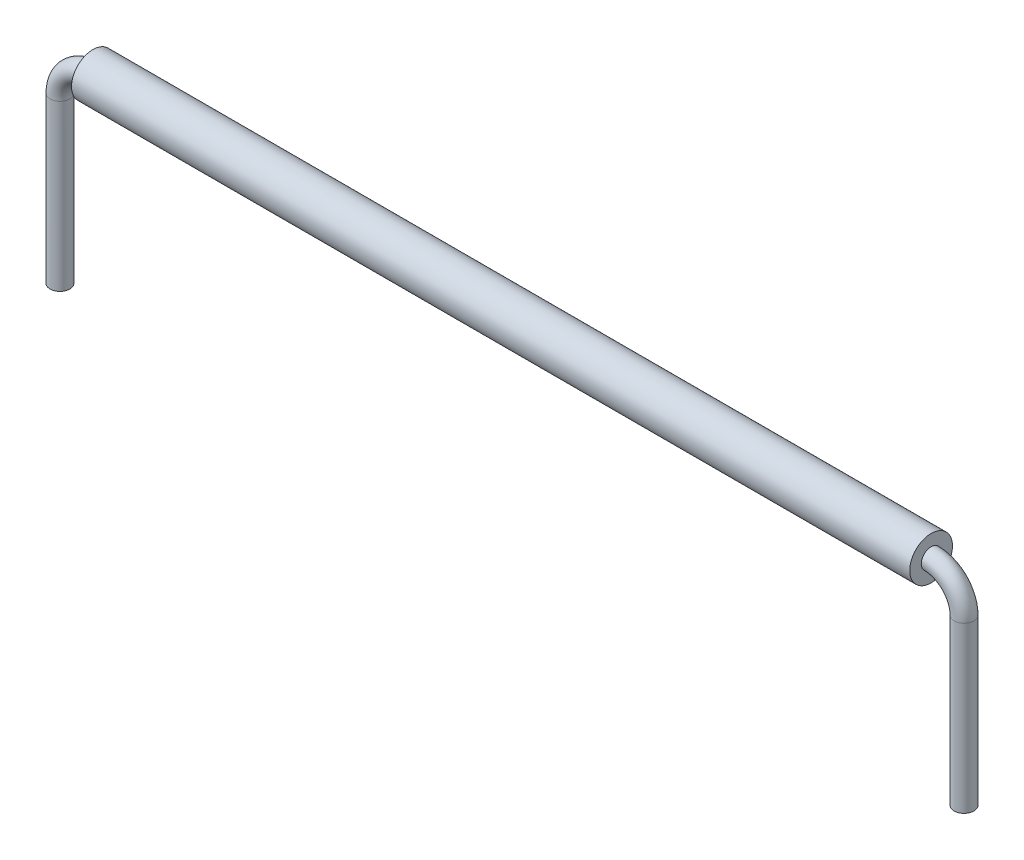
SolidWorks part; units mm, degrees
other "Insulation"
other "Wire"
ref_plane "Front Plane" through (0, 0, 0) normal (0, 0, 1) x (1, 0, 0)
ref_plane "Top Plane" through (0, 0, 0) normal (0, 1, 0) x (1, 0, 0)
ref_plane "Right Plane" through (0, 0, 0) normal (1, 0, 0) x (0, 0, -1)
sketch "Sketch1" plane through (0, 0, 0) normal (0, 0, 1) x (1, 0, 0)
  line L0 (-12.7275, 0) -> (12.7275, 0)
  line L1 (-13.7275, -1) -> (-13.7275, -6)
  line L2 (13.7275, -1) -> (13.7275, -6)
  line L3 (0, 0) -> (0, -6) construction
  line L4 (-13.7275, -6) -> (13.7275, -6) construction
  arc A0 (-12.7275, 0) -> (-13.7275, -1) centre (-12.7275, -1) ccw
  arc A1 (12.7275, 0) -> (13.7275, -1) centre (12.7275, -1) cw
  dimension "D1" = 1
  dimension "D2" = 27.455
  dimension "D3" = 6
sketch "Sketch2" plane through (0, 0, 0) normal (1, 0, 0) x (0, 0, -1)
  circle A0 centre (0, 0) radius 0.3
  dimension "D1" = 0.6
sweep "Sweep1" add profiles "Sketch2" path "Sketch1"
sketch "Sketch3" plane through (0, 0, 0) normal (1, 0, 0) x (0, 0, -1)
  circle A0 centre (0, 0) radius 0.65
  circle A1 centre (0, 0) radius 0.3
  dimension "D1" = 1.3
  dimension "D2" = 0.6
extrude "Boss-Extrude1" add sketch "Sketch3" along normal up to vertex (12.7275 mm away) and the other way up to vertex (12.7275 mm away) separate body up to point (12.7275, 0, 0) other way up to point (-12.7275, 0, 0)
